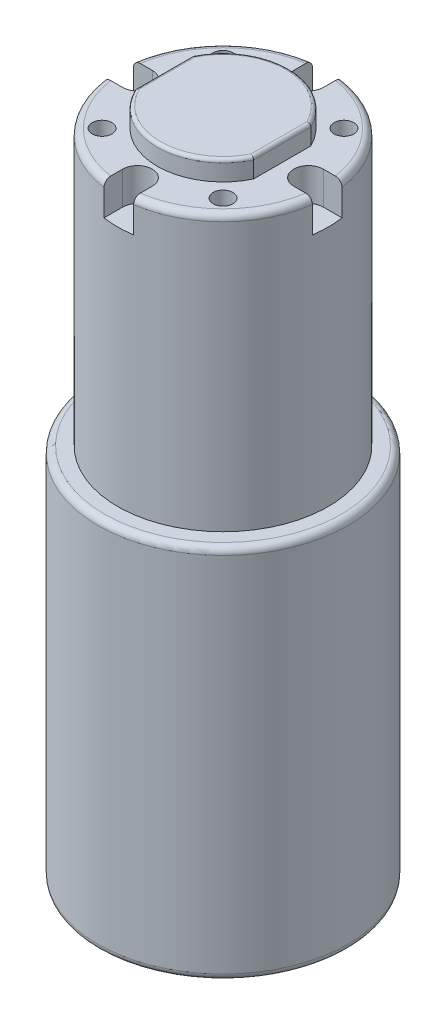
SolidWorks part; units mm, degrees
ref_plane "Front Plane" through (0, 0, 0) normal (0, 0, 1) x (1, 0, 0)
ref_plane "Top Plane" through (0, 0, 0) normal (0, 1, 0) x (1, 0, 0)
ref_plane "Right Plane" through (0, 0, 0) normal (1, 0, 0) x (0, 0, -1)
sketch "Sketch3" plane through (0, 0, 0) normal (0, 1, 0) x (1, 0, 0)
  circle A0 centre (0, 0) radius 3
  dimension "D1" = 6
sketch "Sketch5" plane through (0, 0, 0) normal (0, 1, 0) x (1, 0, 0)
  line L1 (-9, -4.3589) -> (-9, 4.3589)
  line L2 (9, -4.3589) -> (9, 4.3589)
  arc A0 (-9, -4.3589) -> (9, -4.3589) centre (0, 0) ccw
  arc A1 (9, 4.3589) -> (-9, 4.3589) centre (0, 0) ccw
  point P6 (0, 0)
  point P9 (-9, 0)
  point P12 (9, 0)
extrude "Boss-Extrude3" add sketch "Sketch5" against normal blind 3
ref_plane "Plane3" through (0, -3, 0) normal (0, -1, 0) x (-1, 0, 0)
sketch "Sketch7" plane through (0, -3, 0) normal (0, -1, 0) x (-1, 0, 0)
  circle A0 centre (0, 0) radius 13 construction
  circle A1 centre (0, 0) radius 16
extrude "Boss-Extrude4" add sketch "Sketch7" along normal blind 41.8 contours A1
ref_plane "Plane4" through (0, -44.8, 0) normal (0, -1, 0) x (-1, 0, 0)
sketch "Sketch8" plane through (0, -44.8, 0) normal (0, -1, 0) x (-1, 0, 0)
  circle A0 centre (0, 0) radius 19
extrude "Boss-Extrude5" add sketch "Sketch8" along normal blind 57.1
fillet "Fillet1" radius 1 2 edges at (0, -44.8, -19) (0, -3, -16)
fillet "Fillet2" radius 0.5 4 edges at (-9, 0, 0) (9, 0, 0) (0, 0, 10) (0, 0, -10)
sketch "Sketch9" plane through (0, -3, 0) normal (0, -1, 0) x (-1, 0, 0)
  line L0 (-17.5, -2.25) -> (-17.5, 2.25)
  line L1 (2.25, -17.5) -> (-2.25, -17.5)
  line L2 (2.25, -17.5) -> (2.25, -13)
  line L3 (-17.5, -2.25) -> (-13, -2.25)
  line L4 (-2.25, -17.5) -> (-2.25, -13)
  line L5 (-17.5, 2.25) -> (-13, 2.25)
  line L6 (-2.25, 17.5) -> (2.25, 17.5)
  line L7 (-2.25, 17.5) -> (-2.25, 13)
  line L8 (2.25, 17.5) -> (2.25, 13)
  line L9 (17.5, 2.25) -> (17.5, -2.25)
  line L10 (17.5, 2.25) -> (13, 2.25)
  line L11 (17.5, -2.25) -> (13, -2.25)
  arc A0 (2.2416, -12.8053) -> (-2.2416, -12.8053) centre (0, 0) ccw construction
  arc A1 (2.25, -13) -> (-2.25, -13) centre (0, -13) ccw
  arc A2 (-13, -2.25) -> (-13, 2.25) centre (-13, 0) ccw
  arc A3 (-2.25, 13) -> (2.25, 13) centre (0, 13) ccw
  arc A4 (13, 2.25) -> (13, -2.25) centre (13, 0) ccw
  circle A5 centre (9.1924, -9.1924) radius 1.5
  circle A6 centre (-9.1924, -9.1924) radius 1.5
  circle A7 centre (-9.1924, 9.1924) radius 1.5
  circle A8 centre (9.1924, 9.1924) radius 1.5
  point P5 (0, -15.25)
  point P14 (-15.25, 0)
  point P20 (0, 15.25)
  point P26 (15.25, 0)
  point P31 (0, 0)
  point P40 (0, 0)
  dimension "D1" = 4
  dimension "D2" = 4
extrude "Cut-Extrude2" cut sketch "Sketch9" along normal blind 5
fillet "Fillet3" radius 1 1 edges at (0, -101.9, -19)
